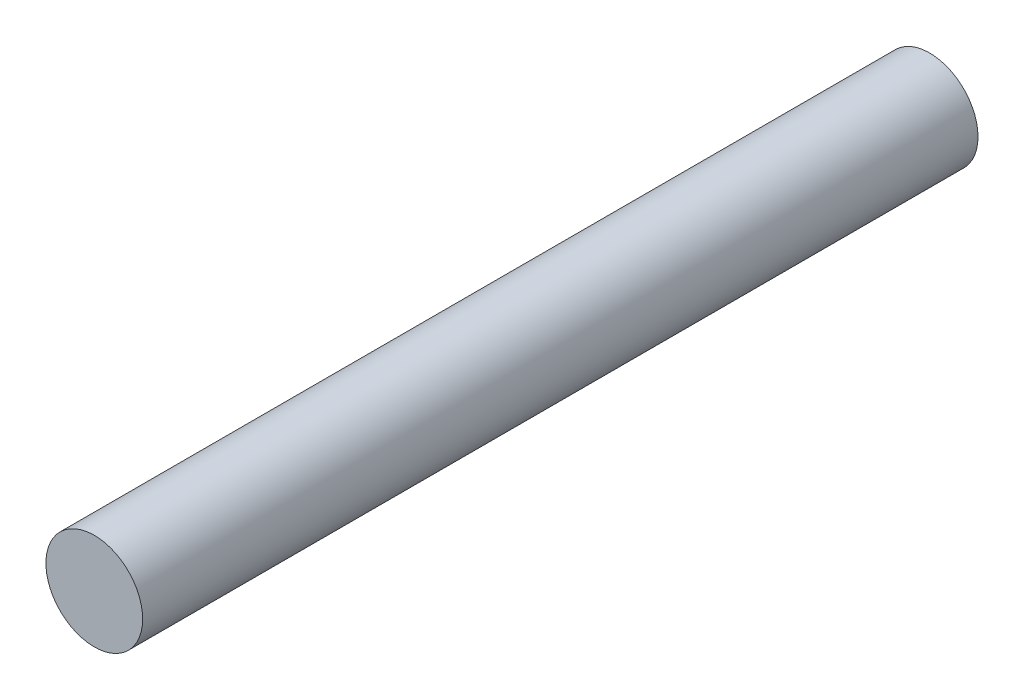
SolidWorks part; units mm, degrees
ref_plane "Front Plane" through (0, 0, 0) normal (0, 0, 1) x (1, 0, 0)
ref_plane "Top Plane" through (0, 0, 0) normal (0, 1, 0) x (1, 0, 0)
ref_plane "Right Plane" through (0, 0, 0) normal (1, 0, 0) x (0, 0, -1)
sketch "Sketch1" plane through (0, 0, 0) normal (0, 0, 1) x (1, 0, 0)
  circle A0 centre (0, 0) radius 2.9139
  dimension "D1" = 5.8278
extrude "Boss-Extrude1" add sketch "Sketch1" along normal blind 50.3311
